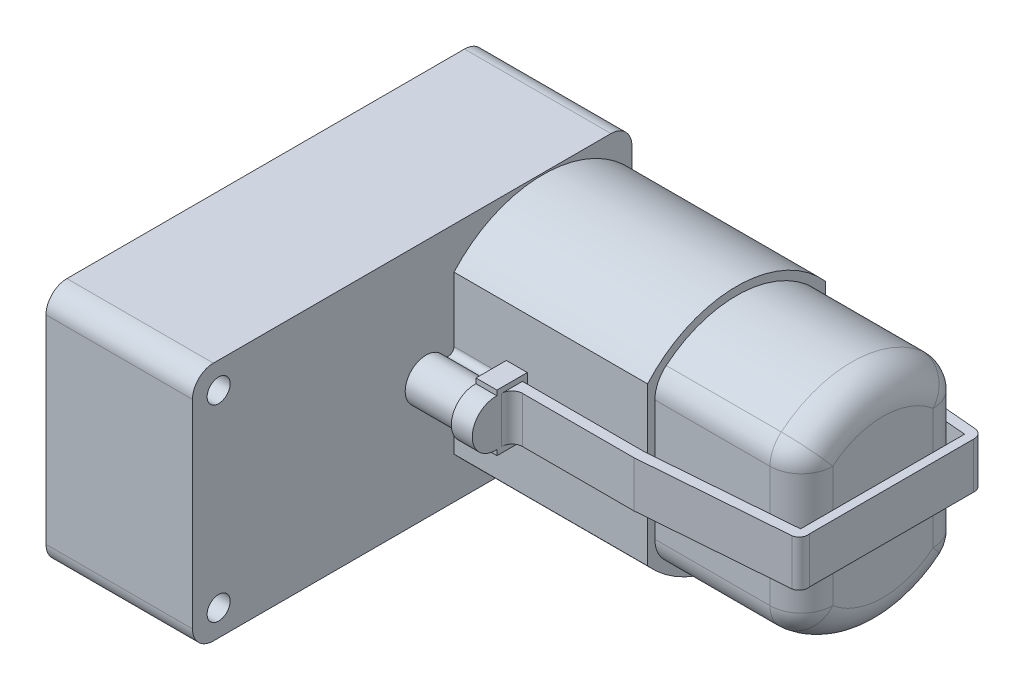
SolidWorks part; units mm, degrees
ref_plane "Front Plane" through (0, 0, 0) normal (0, 0, 1) x (1, 0, 0)
ref_plane "Top Plane" through (0, 0, 0) normal (0, 1, 0) x (1, 0, 0)
ref_plane "Right Plane" through (0, 0, 0) normal (1, 0, 0) x (0, 0, -1)
sketch "Sketch1" plane through (0, 0, 0) normal (0, 1, 0) x (1, 0, 0)
  line L1 (-21.7296, 20.5432) -> (-7.7296, 20.5432)
  line L2 (-21.7296, 20.5432) -> (-21.7296, -21.4568)
  line L3 (-21.7296, -21.4568) -> (-7.7296, -21.4568)
  line L4 (-7.7296, 20.5432) -> (-7.7296, -21.4568)
  dimension "D1" = 42
  dimension "D2" = 14
extrude "Main Body" add sketch "Sketch1" along normal blind 23
fillet "Fillet1" radius 2 4 edges at (-14.7296, 23, -20.5432) (-14.7296, 0, -20.5432) (-14.7296, 0, 21.4568) (-14.7296, 23, 21.4568)
sketch "Sketch2" plane through (-7.7296, 0, 0) normal (1, 0, 0) x (0, 0, -1)
  line L2 (3.5432, 19.0333) -> (3.5432, 3.9667)
  line L4 (20.5432, 19.0333) -> (20.5432, 3.9667)
  line L5 (20.5432, 21) -> (20.5432, 2) construction
  line L6 (-996.4568, 11.5) -> (49003.5432, 11.5) construction
  line L7 (12.0432, -977) -> (12.0432, 49023) construction
  arc A0 (20.5432, 19.0333) -> (3.5432, 19.0333) centre (12.0432, 11.5) ccw
  arc A1 (3.5432, 3.9667) -> (20.5432, 3.9667) centre (12.0432, 11.5) ccw
  point P11 (3.5432, 11.5)
extrude "Motor Holder" add sketch "Sketch2" along normal blind 18.5
sketch "Sketch3" plane through (-7.7296, 0, 0) normal (1, 0, 0) x (0, 0, -1)
  line L0 (3.5432, 11.5) -> (-4.3884, 11.5) construction
  line L1 (3.5432, 19.0333) -> (3.5432, 3.9667) construction
  line L2 (3.5432, 19.0333) -> (3.5432, 3.9667) construction
  line L3 (3.5432, 12.8669) -> (3.5432, 10.3277)
  arc A0 (2.5583, 12.5817) -> (2.6054, 10.4953) centre (0.876, 11.5) ccw
  arc A1 (2.5583, 12.5817) -> (3.5432, 12.8669) centre (3.0065, 12.8772) ccw
  arc A2 (2.6054, 10.4953) -> (3.5432, 10.3277) centre (3.0401, 10.2201) cw
extrude "Boss-Extrude3" add sketch "Sketch3" along normal blind 5
sketch "Sketch4" plane through (-7.7296, 0, 0) normal (1, 0, 0) x (0, 0, -1)
  line L0 (-18.9568, -979.1157) -> (-18.9568, 49020.8843) construction
  line L1 (-19.4568, 23) -> (18.5432, 23) construction
  line L2 (-21.4568, 21) -> (-21.4568, 2) construction
  line L3 (-19.4568, 0) -> (18.5432, 0) construction
  circle A0 centre (-18.9568, 20.5) radius 1.1
  circle A1 centre (-18.9568, 2.5) radius 1.1
  dimension "D1" = 2.5
  dimension "D2" = 2.5
  dimension "D3" = 2.5
extrude "Nut Holes" cut sketch "Sketch4" against normal blind 15
sketch "Sketch5" plane through (0, 0, -20.5432) normal (0, 0, -1) x (-1, 0, 0)
  line L0 (7.7296, 19.0333) -> (7.7296, 3.9667) construction
  line L2 (6.7296, 9.5) -> (8.7296, 9.5)
  line L3 (6.7296, 9.5) -> (6.7296, 13.5)
  line L4 (6.7296, 13.5) -> (8.7296, 13.5)
  line L5 (8.7296, 9.5) -> (8.7296, 13.5)
  line L6 (6.7296, 9.5) -> (8.7296, 13.5) construction
  line L7 (6.7296, 13.5) -> (8.7296, 9.5) construction
  point P4 (7.7296, 11.5)
  dimension "D1" = 2
  dimension "D2" = 4
extrude "Boss-Extrude4" add sketch "Sketch5" along normal blind 5
sketch "Sketch6" plane through (-6.7296, 0, 0) normal (1, 0, 0) x (0, 0, -1)
  line L0 (25.5432, 13.5) -> (25.5432, 9.5) construction
  line L1 (20.5432, 3.9667) -> (20.5432, 19.0333) construction
  line L2 (20.5432, 13.5) -> (20.5432, 9.5) construction
  circle A0 centre (23.5432, 11.5) radius 2
  arc A1 (21.6793, 12.2253) -> (20.5432, 12.2253) centre (21.1113, 12.3852) cw
  arc A2 (21.6793, 10.7747) -> (20.5432, 10.7747) centre (21.1113, 10.5279) ccw
  line M1 (20.5432, 13.5) -> (20.5432, 9.5)
extrude "Boss-Extrude5" add sketch "Sketch6" along normal up to vertex (4 mm away) contours A0 A1 | A2 A0 A1 M1
sketch "Sketch7" plane through (-6.7296, 0, 0) normal (1, 0, 0) x (0, 0, -1)
  line L0 (23.5432, 13.5) -> (23.5432, 13.9672)
  line L1 (23.5432, 13.9672) -> (25.7602, 13.9672)
  line L2 (25.7602, 13.9672) -> (25.7602, 8.9705)
  line L3 (25.7602, 8.9705) -> (23.5432, 8.9705)
  line L4 (23.5432, 8.9705) -> (23.5432, 9.5)
  arc A0 (23.5432, 13.5) -> (23.5432, 9.5) centre (23.5432, 11.5) cw
  arc A1 (21.6793, 10.7747) -> (21.6793, 12.2253) centre (23.5432, 11.5) ccw construction
  arc A2 (23.5432, 9.5) -> (25.5432, 11.5) centre (23.5432, 11.5) ccw construction
extrude "Cut-Extrude2" cut sketch "Sketch7" against normal blind 2
sketch "Sketch8" plane through (10.7704, 0, 0) normal (1, 0, 0) x (0, 0, -1)
  line L0 (4.2432, 17.3565) -> (4.2432, 5.8225)
  line L2 (19.8432, 5.8225) -> (19.8432, 17.3565)
  line L4 (3.5432, 19.0333) -> (3.5432, 3.9667) construction
  line L5 (20.5432, 3.9667) -> (20.5432, 19.0333) construction
  arc A0 (5.324, 3.5167) -> (18.7624, 3.5167) centre (12.0432, 11.5895) ccw
  arc A1 (18.7624, 19.6623) -> (5.324, 19.6623) centre (12.0432, 11.5895) ccw
  arc A2 (4.2432, 17.3565) -> (5.324, 19.6623) centre (7.2432, 17.3565) cw
  arc A3 (19.8432, 17.3565) -> (18.7624, 19.6623) centre (16.8432, 17.3565) ccw
  arc A4 (4.2432, 5.8225) -> (5.324, 3.5167) centre (7.2432, 5.8225) ccw
  arc A5 (18.7624, 3.5167) -> (19.8432, 5.8225) centre (16.8432, 5.8225) ccw
  dimension "D3" = 3
  dimension "D1" = 0.7
  dimension "D2" = 0.7
extrude "Boss-Extrude6" add sketch "Sketch8" along normal blind 14
sketch "Sketch9" plane through (-2.7296, 0, 0) normal (1, 0, 0) x (0, 0, -1)
  line L0 (3.5432, 8.7842) -> (0.6451, 14.2207) construction
  line L1 (20.5342, 8.7842) -> (23.4323, 8.7842)
  line L2 (20.5342, 8.7842) -> (20.5342, 14.2207)
  line L3 (20.5342, 14.2207) -> (23.4323, 14.2207)
  line L4 (23.4323, 8.7842) -> (23.4323, 9.2638)
  line L5 (20.5342, 8.7842) -> (23.4323, 14.2207) construction
  line L6 (20.5342, 14.2207) -> (23.4323, 8.7842) construction
  line L7 (3.5432, 14.2207) -> (0.6451, 8.7842) construction
  line L8 (3.5432, 8.7842) -> (0.6451, 8.7842)
  line L9 (0.6451, 14.2207) -> (0.6451, 13.741)
  line L10 (3.5432, 14.2207) -> (3.5432, 8.7842)
  line L11 (3.5432, 14.2207) -> (0.6451, 14.2207)
  line L12 (0.6451, 9.2942) -> (0.6451, 8.7842)
  line L13 (23.4323, 13.7107) -> (23.4323, 14.2207)
  arc A0 (23.4323, 13.7107) -> (23.4323, 9.2638) centre (23.5637, 11.4873) cw
  arc A1 (0.6451, 9.2942) -> (0.6451, 13.741) centre (0.5138, 11.5176) cw
  point P0 (21.9833, 11.5024)
  point P8 (2.0942, 11.5024)
  arc M1 (21.6793, 10.7747) -> (21.6793, 12.2253) centre (23.5432, 11.5) ccw
  arc M2 (21.6793, 12.2253) -> (20.5432, 12.2253) centre (21.1113, 12.3852) cw
  line M3 (20.5432, 12.2253) -> (20.5432, 10.7747)
  arc M4 (20.5432, 10.7747) -> (21.6793, 10.7747) centre (21.1113, 10.5279) cw
extrude "Boss-Extrude7" add sketch "Sketch9" along normal blind 2 contours A0 L4 M1 | L4 M1 | L1 L4 L3 L2 M1 M4 M3 M2 | L4 M1 M2 M3 M4 | A1 L12 L8 L10 L11 L9
fillet "Fillet2" radius 3 8 edges at (24.7704, 18.6297, -19.5596) (24.7704, 11.5895, -19.8432) (24.7704, 4.5492, -19.5596) (24.7704, 1.0863, -12.0432) (24.7704, 4.5492, -4.5268) (24.7704, 11.5895, -4.2432) (24.7704, 18.6297, -4.5268) (24.7704, 22.0927, -12.0432)
sketch3d "3DSketch2" plane through (0, 0, 0) normal (0, 0, 1) x (1, 0, 0)
  dimension "D1" = 11.5176
sketch "Sketch10" plane through (0, 11.5176, 0) normal (0, 1, 0) x (1, 0, 0)
  line L0 (-0.7296, 20.5432) -> (-0.7296, 23.4323) construction
  line L1 (-0.7296, 21.9878) -> (10.9103, 21.9878)
  line L2 (-0.7296, 21.9878) -> (-0.7296, 21.0215)
  line L3 (-0.7296, 21.0215) -> (10.9103, 21.0215)
  line L5 (-0.7296, 3.5432) -> (-0.7296, 0.6451) construction
  line L6 (-0.7296, 2.0942) -> (10.9103, 2.0942)
  line L7 (-0.7296, 2.0942) -> (-0.7296, 3.0856)
  line L8 (-0.7296, 3.0856) -> (10.9103, 3.0856)
  line L10 (24.7704, 19.8432) -> (10.9103, 21.0215)
  line L12 (24.7704, 19.8432) -> (24.7704, 4.1661)
  line L14 (25.6047, 19.8432) -> (25.6047, 4.1661)
  line L15 (10.9103, 21.9878) -> (24.7704, 20.8094)
  line L17 (10.9103, 3.0856) -> (24.7704, 4.1661)
  line L18 (10.9103, 2.0942) -> (24.9385, 3.1877)
  arc A0 (24.9385, 3.1877) -> (25.6047, 4.1661) centre (24.7903, 4.0047) ccw
  arc A1 (24.7704, 20.8094) -> (25.6047, 19.8432) centre (24.7158, 19.919) cw
extrude "Boss-Extrude8" add sketch "Sketch10" along normal blind 2.2 and the other way blind 2.2
fillet "Fillet3" radius 1 2 edges at (-0.7296, 11.5176, -2.0942) (-0.7296, 11.5176, -21.9878)
sketch "Sketch12" plane through (-21.7296, 0, 0) normal (-1, 0, 0) x (0, 0, 1)
  line L0 (21.4568, 11.5) -> (10.4568, 11.5) construction
  line L1 (21.4568, 21) -> (21.4568, 2) construction
  circle A0 centre (10.4568, 11.5) radius 3.5
  circle A1 centre (10.4568, 11.5) radius 3.0703
extrude "Boss-Extrude9" add sketch "Sketch12" along normal blind 1
sketch "Sketch14" plane through (-21.7296, 0, 0) normal (-1, 0, 0) x (0, 0, 1)
  circle A0 centre (10.4568, 11.5) radius 3
extrude "Boss-Extrude10" add sketch "Sketch14" along normal blind 1
sketch "Sketch15" plane through (-22.7296, 0, 0) normal (-1, 0, 0) x (0, 0, 1)
  line L2 (8.8483, 8.9677) -> (8.8483, 14.0323)
  line L4 (12.0653, 8.9677) -> (12.0653, 14.0323)
  line L5 (8.8483, 8.9677) -> (12.0653, 14.0323) construction
  line L6 (8.8483, 14.0323) -> (12.0653, 8.9677) construction
  circle A0 centre (10.4568, 11.5) radius 3 construction
  arc A1 (8.8483, 14.0323) -> (12.0653, 14.0323) centre (10.4568, 11.5) cw
  arc A2 (8.8483, 8.9677) -> (12.0653, 8.9677) centre (10.4568, 11.5) ccw
  circle A3 centre (10.4568, 11.5) radius 1
  point P0 (10.4568, 11.5)
  point P1 (10.4568, 11.5)
extrude "Shaft" add sketch "Sketch15" along normal blind 7
sketch "Sketch16" plane through (-21.7296, 0, 0) normal (-1, 0, 0) x (0, 0, 1)
  line L0 (21.4568, 11.5) -> (-0.5432, 11.5) construction
  line L1 (21.4568, 21) -> (21.4568, 2) construction
  circle A0 centre (-0.5432, 11.5) radius 2
extrude "Boss-Extrude12" add sketch "Sketch16" along normal blind 1.5
